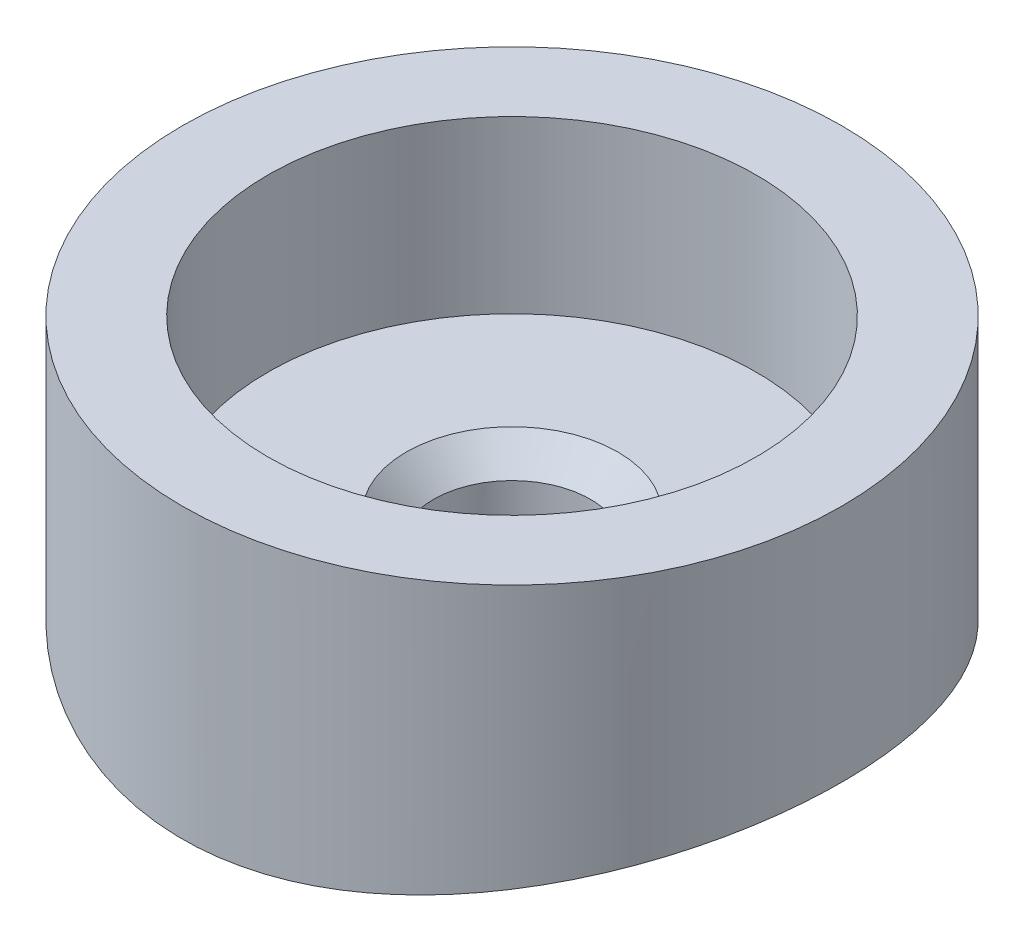
SolidWorks part; units mm, degrees
ref_plane "Front Plane" through (0, 0, 0) normal (0, 0, 1) x (1, 0, 0)
ref_plane "Top Plane" through (0, 0, 0) normal (0, 1, 0) x (1, 0, 0)
ref_plane "Right Plane" through (0, 0, 0) normal (1, 0, 0) x (0, 0, -1)
sketch "Sketch2" plane through (0, 0, 0) normal (0, 1, 0) x (1, 0, 0)
  circle A0 centre (0, 0) radius 24.511
extrude "Boss-Extrude2" add sketch "Sketch2" along normal blind 25.4
sketch "Sketch3" plane through (0, 25.4, 0) normal (0, 1, 0) x (1, 0, 0)
  circle A0 centre (0, 0) radius 18.161
extrude "Cut-Extrude1" cut sketch "Sketch3" against normal blind 12.7 contours A0
sketch "Sketch11" plane through (0, 0, 0) normal (1, 0, 0) x (0, 0, -1)
  circle A0 centre (0, -76.2) radius 83.82
extrude "Cut-Extrude2" cut sketch "Sketch11" against normal blind 42.926 and the other way blind 41.402
sketch "Sketch13" plane through (0, 12.7, 0) normal (0, 1, 0) x (1, 0, 0)
  circle A0 centre (0, 0) radius 5.842
extrude "Cut-Extrude3" cut sketch "Sketch13" against normal blind 42.926
chamfer "Chamfer1" distance 2.032 angle 45 1 edges at (0, 12.7, 5.842)
sketch3d "3DSketch2"
  circle A0 centre (-1.1071, -71.455, -2.0204) radius 80.5167
  point P2 (-1.1071, -71.455, 78.4964)
